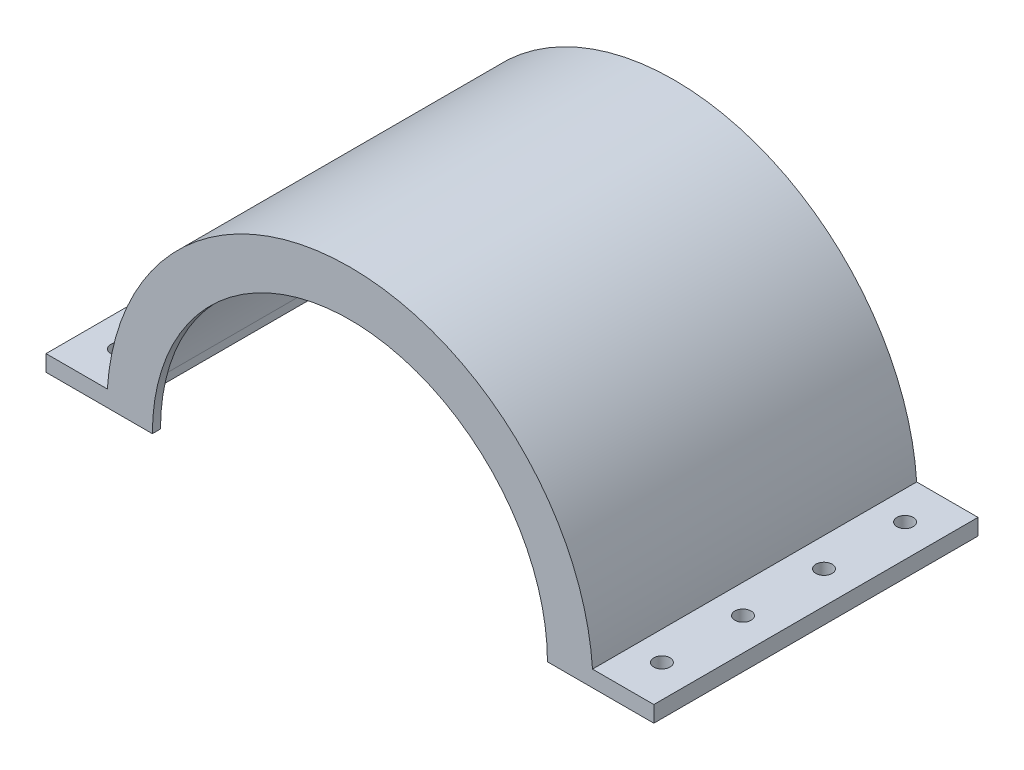
SolidWorks part; units mm, degrees
ref_plane "Front Plane" through (0, 0, 0) normal (0, 0, 1) x (1, 0, 0)
ref_plane "Top Plane" through (0, 0, 0) normal (0, 1, 0) x (1, 0, 0)
ref_plane "Right Plane" through (0, 0, 0) normal (1, 0, 0) x (0, 0, -1)
sketch "Sketch1" plane through (0, 0, 0) normal (0, 0, 1) x (1, 0, 0)
  line L0 (-75, 0) -> (75, 0)
  line L1 (0, 0) -> (0, 73.1042) construction
  line L2 (75, 0) -> (75, 4)
  line L3 (-75, 0) -> (-75, 4)
  line L4 (75, 4) -> (59.8665, 4)
  line L5 (-75, 4) -> (-59.8665, 4)
  arc A0 (59.8665, 4) -> (-59.8665, 4) centre (0, 0) ccw
  dimension "D1" = 120
  dimension "D2" = 75
  dimension "D3" = 73.1042
  dimension "D4" = 4
  dimension "D5" = 15.1335
extrude "Boss-Extrude1" add sketch "Sketch1" along normal blind 80
shell "Shell1" thickness 2
sketch "Sketch2" plane through (0, 2, 0) normal (0, -1, 0) x (1, 0, 0)
  line L1 (-73, 78) -> (-57.9655, 78)
  line L2 (-73, 78) -> (-73, 2)
  line L3 (-73, 2) -> (-57.9655, 2)
  line L4 (-57.9655, 78) -> (-57.9655, 2)
  line L5 (57.9123, 78) -> (73, 78)
  line L6 (57.9123, 78) -> (57.9123, 2)
  line L7 (57.9123, 2) -> (73, 2)
  line L8 (73, 78) -> (73, 2)
  dimension "D1" = 76
  dimension "D2" = 15.0345
  dimension "D3" = 76
  dimension "D4" = 15.0877
extrude "Boss-Extrude2" add sketch "Sketch2" along normal up to surface (2 mm away) up to face at (0, 0, 40)
sketch "Sketch3" plane through (0, 0, 80) normal (0, 0, 1) x (1, 0, 0)
  line L0 (-48.75, 0) -> (48.75, 0)
  arc A0 (48.75, 0) -> (-48.75, 0) centre (0, 0) ccw
  dimension "D2" = 97.5
extrude "Cut-Extrude1" cut sketch "Sketch3" against normal up to next
sketch "Sketch5" plane through (0, 0, 0) normal (0, 0, -1) x (-1, 0, 0)
  line L0 (-15, 0) -> (15, 0)
  arc A0 (15, 0) -> (-15, 0) centre (0, 0) ccw
  dimension "D1" = 30
  dimension "D2" = 30
extrude "Cut-Extrude2" cut sketch "Sketch5" against normal up to next
sketch "Sketch6" plane through (0, 0, 0) normal (0, -1, 0) x (1, 0, 0)
  circle A0 centre (67, 70) radius 2
  dimension "D3" = 4
  dimension "D4" = 67
  dimension "D5" = 70
extrude "Cut-Extrude6" cut sketch "Sketch6" against normal through all
pattern_linear "LPattern1" count 4 spacing 20 along (0, 0, -1) of "Cut-Extrude6"
ref_plane "Plane1" through (0, 0, 0) normal (1, 0, 0) x (0, 0, -1)
mirror "Mirror1" about plane through (0, 0, 0) normal (1, 0, 0) of "LPattern1", "Cut-Extrude6"
ref_plane "Plane2" through (-81.5, 0, 0) normal (1, 0, 0) x (0, 0, -1)
ref_plane "Plane3" through (0, 0, 40) normal (0, 0, 1) x (1, 0, 0)
sketch "Sketch7" plane through (0, 0, 40) normal (0, 0, 1) x (1, 0, 0)
  line L0 (-81.5, -45.1099) -> (-81.5, 45.1099) construction
  line L1 (-39.911, -2.6667) -> (-39.911, 97.3333) construction
  line L3 (59.8665, 4) -> (-39.911, -2.6667) construction
  line L4 (-39.911, 97.3333) -> (-81.5, 97.3333)
  arc A0 (59.8665, 4) -> (-39.911, 97.3333) centre (-39.911, -2.6667) ccw
  point P8 (-81.5, 0)
  point P9 (-81.5, 137.1762)
  dimension "D3" = 100
  dimension "D1" = 97.3333
sketch "Sketch8" plane through (-81.5, 0, 0) normal (1, 0, 0) x (0, 0, -1)
  line L2 (-53.75, 104) -> (-26.25, 104)
  line L3 (-11.25, 89) -> (-11.25, 77)
  line L4 (-68.75, 89) -> (-68.75, 77)
  line L5 (-26.25, 62) -> (-53.75, 62)
  arc A0 (-11.25, 89) -> (-26.25, 104) centre (-26.25, 89) ccw
  arc A1 (-26.25, 62) -> (-11.25, 77) centre (-26.25, 77) ccw
  arc A2 (-68.75, 89) -> (-53.75, 104) centre (-53.75, 89) cw
  arc A3 (-53.75, 62) -> (-68.75, 77) centre (-53.75, 77) cw
  point P9 (-40, 62)
  dimension "D1" = 15
  dimension "D2" = 15
  dimension "D3" = 15
  dimension "D4" = 15
  dimension "D5" = 62
  dimension "D6" = 104
  dimension "D7" = 40
  dimension "D8" = 27.5
sketch "Sketch9" plane through (0, 0, 40) normal (0, 0, 1) x (1, 0, 0)
  line L0 (-50.134, 46.9847) -> (-81.3522, 46.9847)
  dimension "D1" = 31.2182
  dimension "D2" = 50.134
  dimension "D3" = 46.9847
